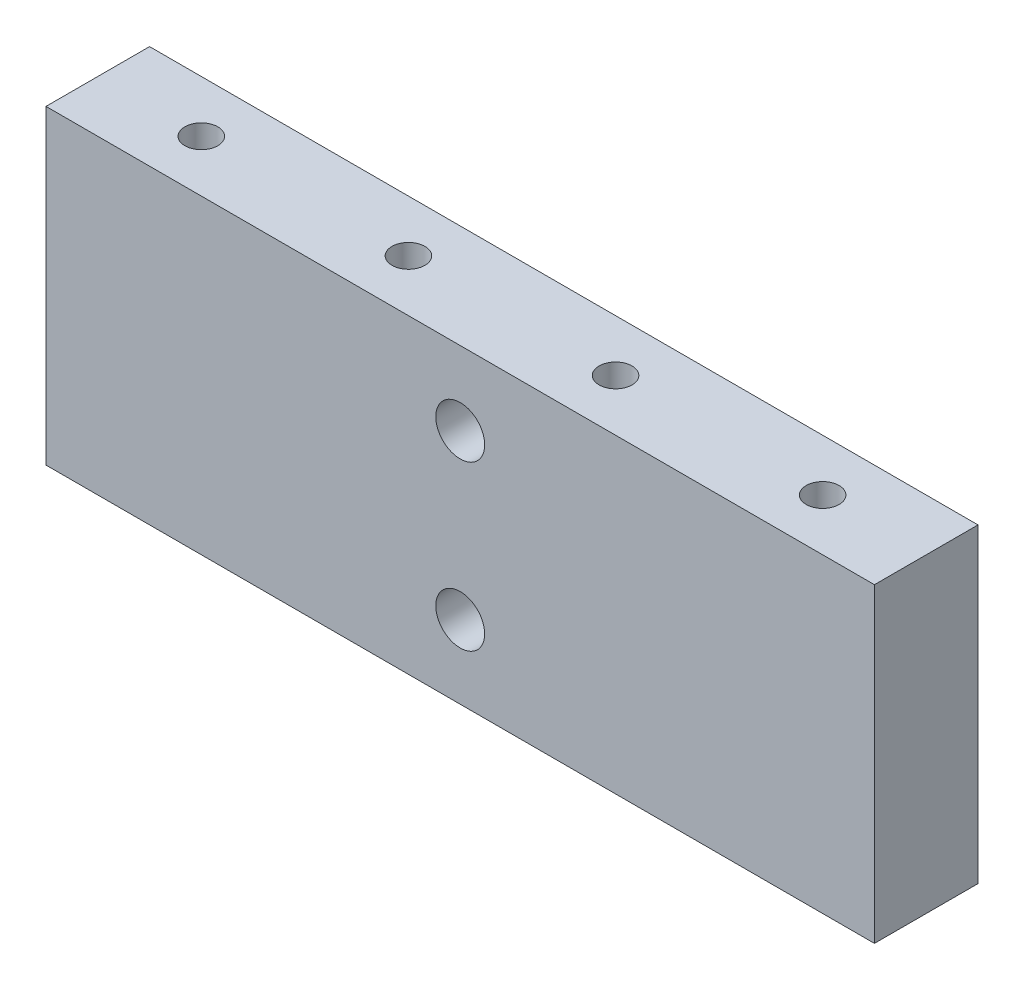
SolidWorks part; units mm, degrees
ref_plane "Front Plane" through (0, 0, 0) normal (0, 0, 1) x (1, 0, 0)
ref_plane "Top Plane" through (0, 0, 0) normal (0, 1, 0) x (1, 0, 0)
ref_plane "Right Plane" through (0, 0, 0) normal (1, 0, 0) x (0, 0, -1)
sketch "Sketch1" plane through (0, 0, 0) normal (0, 0, 1) x (1, 0, 0)
  line L1 (-50.8, 19.05) -> (50.8, 19.05)
  line L2 (-50.8, 19.05) -> (-50.8, -19.05)
  line L3 (-50.8, -19.05) -> (50.8, -19.05)
  line L4 (50.8, 19.05) -> (50.8, -19.05)
  line L5 (-50.8, 19.05) -> (50.8, -19.05) construction
  line L6 (-50.8, -19.05) -> (50.8, 19.05) construction
  point P0 (0, 0)
  dimension "D1" = 101.6
  dimension "D2" = 38.1
extrude "Boss-Extrude1" add sketch "Sketch1" along normal blind 12.7
sketch "Sketch2" plane through (0, 0, 12.7) normal (0, 0, 1) x (1, 0, 0)
  line L0 (0, 19.05) -> (0, -19.05) construction
  line L1 (50.8, 19.05) -> (-50.8, 19.05) construction
  line L2 (-50.8, -19.05) -> (50.8, -19.05) construction
hole_wizard "Ø4.0mm Dowel Hole1" positions "Sketch6" profile "Sketch5" hole size "Ø4.0" standard "ANSI Metric" end condition through all
sketch "Sketch6" plane through (0, 0, 12.7) normal (0, 0, 1) x (1, 0, 0)
  line L0 (0, 19.05) -> (0, -19.05) construction
  line L1 (50.8, 19.05) -> (-50.8, 19.05) construction
  point P0 (0, 10)
  point P4 (0, -10)
  dimension "D1" = 20
  dimension "D2" = 9.05
sketch "Sketch5" plane through (0, 10, 12.7) normal (1, 0, 0) x (0, -1, 0)
  line L0 (0, 0) -> (0, 12.7)
  line L1 (0, 12.7) -> (2, 12.7)
  line L2 (2, 12.7) -> (2, 0)
  line L5 (2, 0) -> (0, 0)
  line L11 (0, -6.35) -> (0, 107.95) construction
  dimension "Thru Hole Dia." = 4
  dimension "Thru Hole Depth" = 12.7
sketch "Sketch7" plane through (0, 0, 12.7) normal (0, 0, 1) x (1, 0, 0)
  line L0 (0, 19.05) -> (0, -19.05) construction
  circle A0 centre (0, -10.0795) radius 2.9972
  circle A1 centre (0, 10) radius 2.9972
  dimension "D1" = 5.9944
extrude "Cut-Extrude1" cut sketch "Sketch7" against normal blind 5.08
hole_wizard "#10-32 Tapped Hole1" positions "Sketch11" profile "Sketch10" tap size "#10-32" standard "ANSI Inch" end condition through all
sketch "Sketch11" plane through (0, 19.05, 0) normal (0, 1, 0) x (1, 0, 0)
  line L0 (-50.8, -6.35) -> (50.8, -6.35) construction
  line L1 (-50.8, -12.7) -> (-50.8, 0) construction
  line L2 (50.8, -12.7) -> (50.8, 0) construction
  point P0 (38.1, -6.35)
  point P2 (12.7, -6.35)
  point P4 (-12.7, -6.35)
  point P6 (-38.1, -6.35)
  dimension "D1" = 12.7
  dimension "D2" = 12.7
  dimension "D3" = 25.4
  dimension "D4" = 25.4
sketch "Sketch10" plane through (38.1, 19.05, 6.35) normal (1, 0, 0) x (0, 0, 1)
  line L0 (0, 0) -> (0, 38.1)
  line L1 (0, 38.1) -> (2.0193, 38.1)
  line L2 (2.0193, 38.1) -> (2.0193, 0)
  line L5 (2.0193, 0) -> (0, 0)
  line L11 (0, -6.35) -> (0, 107.95) construction
  dimension "Thread Major Dia." = 4.0386
  dimension "Thru Tap Drill Depth" = 38.1
